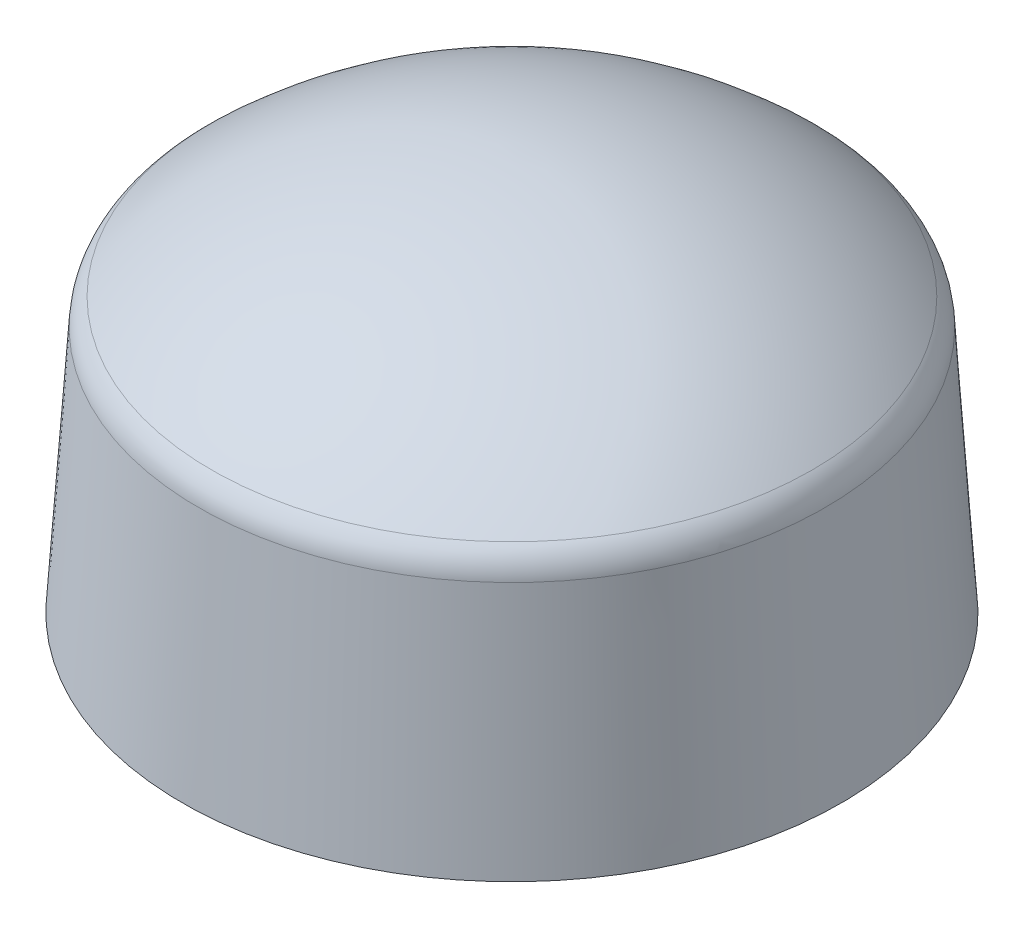
SolidWorks part; units mm, degrees
ref_plane "Front Plane" through (0, 0, 0) normal (0, 0, 1) x (1, 0, 0)
ref_plane "Top Plane" through (0, 0, 0) normal (0, 1, 0) x (1, 0, 0)
ref_plane "Right Plane" through (0, 0, 0) normal (1, 0, 0) x (0, 0, -1)
sketch "Sketch1" plane through (0, 0, 0) normal (0, 0, 1) x (1, 0, 0)
  line L0 (0, 0) -> (0, 14.2947) construction
  line L1 (0, 0) -> (-20, 0) construction
  line L2 (-7.9909, -3.6444) -> (-8.41, -9.96)
  line L5 (0, -1.28) -> (0, 0)
  line L6 (-8.41, -9.96) -> (-6.89, -9.96)
  line L7 (-6.89, -9.96) -> (-6.79, -9.96)
  line L8 (-6.79, -9.96) -> (-6.79, -9.46)
  line L9 (-6.79, -9.46) -> (-7.29, -9.46)
  line L10 (-7.29, -9.46) -> (-6.934, -4.0956)
  arc A0 (0, 0) -> (-7.6671, -2.9718) centre (0, -11.3761) ccw
  arc A1 (-6.8846, -3.9914) -> (0, -1.28) centre (0, -11.3761) cw
  arc A2 (-7.6671, -2.9718) -> (-7.9909, -3.6444) centre (-6.9931, -3.7106) ccw
  arc A3 (-6.8846, -3.9914) -> (-6.934, -4.0956) centre (-6.7777, -4.1059) ccw
  point P13 (-7.965, -3.2536)
  dimension "D8" = 1
  dimension "D9" = 0.5
  dimension "D10" = 6.2494
  dimension "D1" = 20
  dimension "D2" = 1.62
  dimension "D3" = 8.68
  dimension "D4" = 8.41
  dimension "D5" = 7.965
  dimension "D6" = 9.96
  dimension "D7" = 0.5
revolve "Revolve1" add sketch "Sketch1" angle 360 about L0
